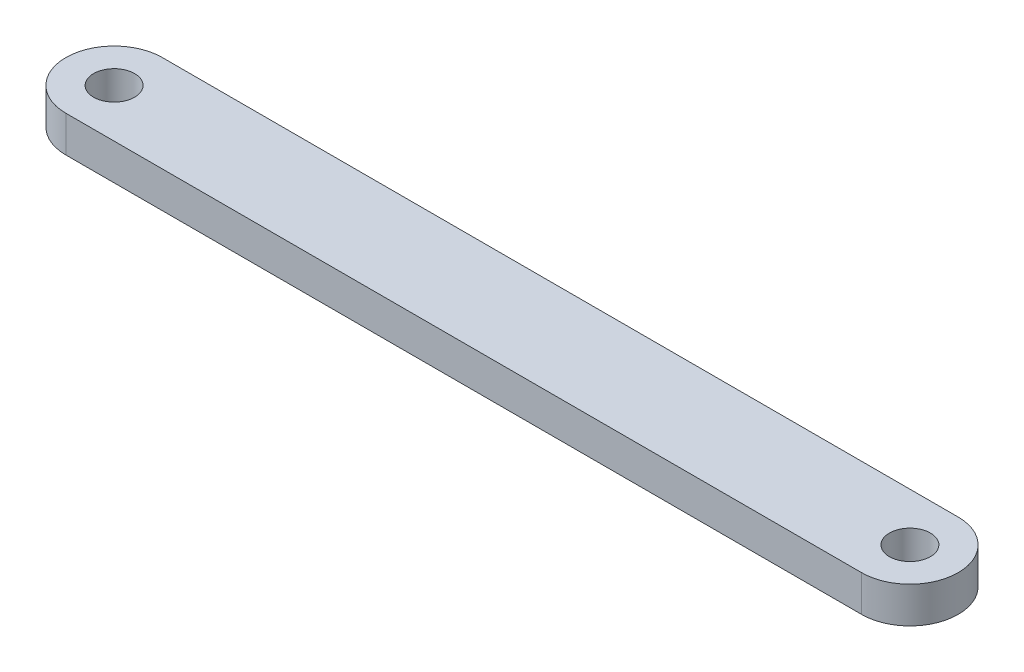
SolidWorks part; units mm, degrees
ref_plane "前视基准面" through (0, 0, 0) normal (0, 0, 1) x (1, 0, 0)
ref_plane "上视基准面" through (0, 0, 0) normal (0, 1, 0) x (1, 0, 0)
ref_plane "右视基准面" through (0, 0, 0) normal (1, 0, 0) x (0, 0, -1)
sketch "草图1" plane through (0, 0, 0) normal (0, 1, 0) x (1, 0, 0)
  line L0 (0, 0) -> (0, 30.7151) construction
  line L1 (-33, 0) -> (33, 0) construction
  line L2 (-33, 4) -> (33, 4)
  line L3 (-33, -4) -> (33, -4)
  arc A0 (-33, 4) -> (-33, -4) centre (-33, 0) ccw
  arc A1 (33, -4) -> (33, 4) centre (33, 0) ccw
  circle A2 centre (-33, 0) radius 1.7
  circle A3 centre (33, 0) radius 1.7
  dimension "D1" = 3.4
  dimension "D2" = 8
  dimension "D3" = 66
extrude "凸台-拉伸1" add sketch "草图1" along normal blind 3
